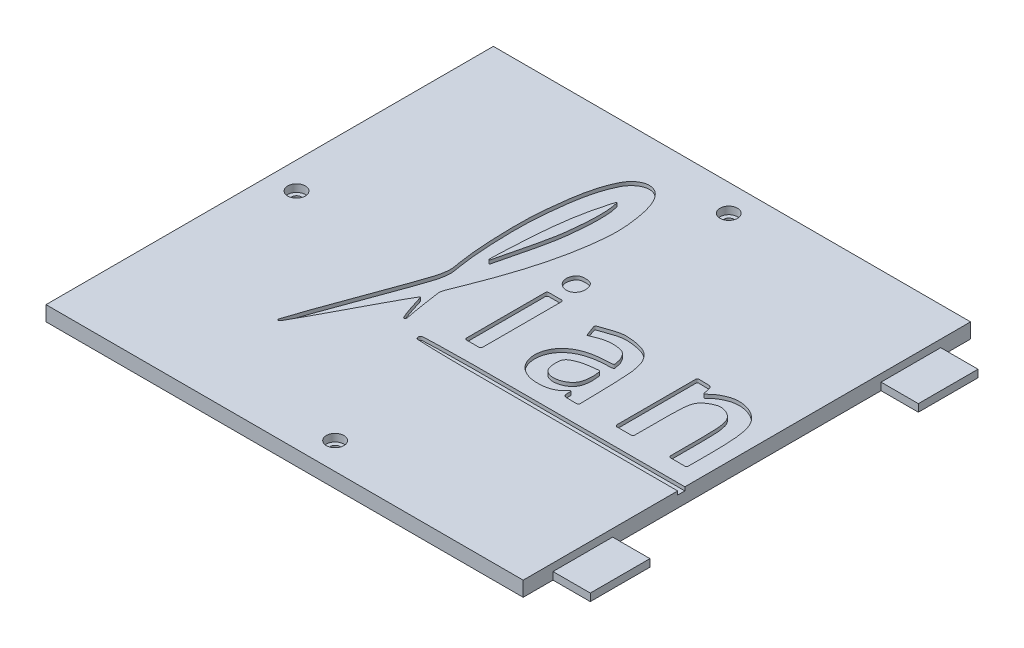
SolidWorks part; units mm, degrees
other "Marca1"
sketch "Croquis4" plane through (-24, 5, 75) normal (0.0144, 0.9293, 0.3691) x (0.9999, -0.0163, 0.0019)
material "PLA"
ref_plane "Alzado" through (0, 0, 0) normal (0, 0, 1) x (1, 0, 0)
ref_plane "Planta" through (0, 0, 0) normal (0, 1, 0) x (1, 0, 0)
ref_plane "Vista lateral" through (0, 0, 0) normal (1, 0, 0) x (0, 0, -1)
sketch "Croquis1" plane through (0, 0, 0) normal (0, 1, 0) x (1, 0, 0)
  line L0 (-327.9437, 75) -> (-327.9437, -75)
  line L1 (-327.9437, 75) -> (-27.9437, 75)
  line L2 (-27.9437, 75) -> (-24, 71.0563)
  line L3 (-327.9437, -75) -> (-27.9437, -75)
  line L4 (-27.9437, -75) -> (-24, -71.0563)
  circle A0 centre (0, 0) radius 75 construction
  arc A1 (-24, 71.0563) -> (-24, -71.0563) centre (0, 0) ccw
  point P0 (0, 0)
  point P6 (-327.9437, 0)
  point P11 (-75, 0)
  point P12 (0, 0)
  dimension "D1" = 150
  dimension "D2" = 150
  dimension "D3" = 300
  dimension "D4" = 135
  dimension "D5" = 24
extrude "Saliente-Extruir1" add sketch "Croquis1" along normal blind 5 contours L1 L2 A1 L4 L3 L0
sketch "Croquis2" plane through (0, 5, 0) normal (0, 1, 0) x (1, 0, 0)
  line L0 (-327.9437, 75) -> (-27.9437, 75) construction
  line L1 (-327.9437, -75) -> (-27.9437, -75) construction
  line L2 (-327.9437, 75) -> (-327.9437, -75) construction
  circle A0 centre (-318.9437, 0) radius 1.6
  circle A1 centre (-240.0037, 66) radius 1.6
  circle A2 centre (-240.0037, -66) radius 1.6
  circle A3 centre (-80.0037, -66) radius 1.6
  circle A4 centre (-80.0037, 66) radius 1.6
  point P10 (0, 0)
  point P12 (0, 0)
  point P13 (0, 0)
  point P14 (0, 0)
  point P15 (0, 0)
  dimension "D1" = 3.2
  dimension "D2" = 9
  dimension "D3" = 9
  dimension "D4" = 9
  dimension "D5" = 160
  dimension "D6" = 87.94
extrude "Cortar-Extruir1" cut sketch "Croquis2" against normal blind 5
sketch "Croquis3" plane through (0, 5, 0) normal (0, 1, 0) x (1, 0, 0)
  circle A0 centre (-240.0037, -66) radius 2.95
  circle A1 centre (-80.0037, -66) radius 2.95
  circle A2 centre (-80.0037, 66) radius 2.95
  circle A3 centre (-240.0037, 66) radius 2.95
  circle A4 centre (-318.9437, 0) radius 2.95
  dimension "D1" = 5.9
extrude "Cortar-Extruir2" cut sketch "Croquis3" against normal blind 2.5
sketch "Croquis5" plane through (0, 5, 0) normal (0, 1, 0) x (1, 0, 0)
  spline S0 degree 3 number of poles 565 (-264.8912, -10.407) -> (-264.8912, -10.407)
  spline S1 degree 3 number of poles 279 (-262.6484, 48.2089) -> (-262.6484, 48.2089)
  spline S2 degree 3 number of poles 493 (-213.5311, -14.7576) -> (-213.5311, -14.7576)
  spline S3 degree 3 number of poles 157 (-225.2653, -4.52) -> (-225.2653, -4.52)
  spline S4 degree 3 number of poles 343 (-98.8163, -23.8618) -> (-98.8163, -23.8618)
  spline S5 degree 3 number of poles 343 (-189.9262, 10.8546) -> (-189.9262, 10.8546)
  spline S6 degree 3 number of poles 380 (-145.717, -14.6405) -> (-145.717, -14.6405)
  spline S7 degree 3 number of poles 125 (-156.8594, -5.2926) -> (-156.8594, -5.2926)
  spline S8 degree 3 number of poles 123 (-242.4618, 21.9905) -> (-242.4618, 21.9905)
  spline S9 degree 3 poles (-242.3565, -0.9911) (-242.3565, 3.3839) (-242.3565, 7.7589) (-242.3565, 12.1339) (-242.3565, 12.24) (-242.3565, 12.4521) (-242.7133, 12.8089) (-242.9254, 12.8089) (-243.0315, 12.8089) (-243.7065, 12.8089) (-244.3815, 12.8089) (-245.0565, 12.8089) (-245.7315, 12.8089) (-246.4065, 12.8089) (-247.0815, 12.8089) (-247.1876, 12.8089) (-247.3997, 12.8089) (-247.7565, 12.4521) (-247.7565, 12.24) (-247.7565, 12.1339) (-247.7565, 7.7589) (-247.7565, 3.3839) (-247.7565, -0.9911) (-247.7565, -5.3661) (-247.7565, -9.7411) (-247.7565, -14.1161) (-247.7565, -14.2221) (-247.7565, -14.4343) (-247.3997, -14.7911) (-247.1876, -14.7911) (-247.0815, -14.7911) (-246.4065, -14.7911) (-245.7315, -14.7911) (-245.0565, -14.7911) (-244.3815, -14.7911) (-243.7065, -14.7911) (-243.0315, -14.7911) (-242.9254, -14.7911) (-242.7133, -14.7911) (-242.3565, -14.4343) (-242.3565, -14.2221) (-242.3565, -14.1161) (-242.3565, -9.7411) (-242.3565, -5.3661) (-242.3565, -0.9911) (-242.3565, 3.3839) (-242.3565, 7.7589) knots -0.203746 0 0 0 0.203746 0.203746 0.203746 0.208686 0.213625 0.218565 0.218565 0.218565 0.25 0.25 0.25 0.281435 0.281435 0.281435 0.286375 0.291314 0.296254 0.296254 0.296254 0.5 0.5 0.5 0.703746 0.703746 0.703746 0.708686 0.713625 0.718565 0.718565 0.718565 0.75 0.75 0.75 0.781435 0.781435 0.781435 0.786375 0.791314 0.796254 0.796254 0.796254 1 1 1 1.203746 1.203746 1.203746 only from (-242.3565, -0.9911) to (-242.3565, -0.9911)
  spline S10 degree 3 number of poles 99 (-100.9338, -21.7323) -> (-100.9338, -21.7323)
extrude "Cortar-Extruir3" cut sketch "Croquis5" against normal blind 1.2
sketch "Croquis6" plane through (0, 5, 0) normal (0, 1, 0) x (1, 0, 0)
  line L0 (-327.9437, 75) -> (-327.9437, -75) construction
  line L1 (-167.9437, -104.5928) -> (32.0563, -104.5928)
  line L2 (-167.9437, -104.5928) -> (-167.9437, 95.4072)
  line L3 (-167.9437, 95.4072) -> (32.0563, 95.4072)
  line L4 (32.0563, -104.5928) -> (32.0563, 95.4072)
  line L5 (-167.9437, -104.5928) -> (32.0563, 95.4072) construction
  line L6 (-167.9437, 95.4072) -> (32.0563, -104.5928) construction
  point P0 (-67.9437, -4.5928)
  point P5 (-278.3273, 0)
  point P8 (-367.9437, 95.4072)
  dimension "D1" = 160
  dimension "D2" = 200
  dimension "D3" = 200
extrude "Cortar-Extruir4" cut sketch "Croquis6" against normal blind 10
sketch "Croquis7" plane through (0, 0, 0) normal (0, -1, 0) x (1, 0, 0)
  line L0 (-167.9437, -75) -> (-167.9437, 75) construction
  line L1 (-180.4437, 65) -> (-155.4437, 65)
  line L2 (-180.4437, 65) -> (-180.4437, 45)
  line L3 (-180.4437, 45) -> (-155.4437, 45)
  line L4 (-155.4437, 65) -> (-155.4437, 45)
  line L5 (-180.4437, 65) -> (-155.4437, 45) construction
  line L6 (-180.4437, 45) -> (-155.4437, 65) construction
  line L7 (-327.9437, 75) -> (-167.9437, 75) construction
  line L8 (-180.4437, -45) -> (-155.4437, -45)
  line L9 (-180.4437, -45) -> (-180.4437, -65)
  line L10 (-180.4437, -65) -> (-155.4437, -65)
  line L11 (-155.4437, -45) -> (-155.4437, -65)
  line L12 (-180.4437, -45) -> (-155.4437, -65) construction
  line L13 (-180.4437, -65) -> (-155.4437, -45) construction
  line L15 (-327.9437, -75) -> (-167.9437, -75) construction
  point P0 (-167.9437, 55)
  point P7 (-167.9437, -55)
  dimension "D1" = 20
  dimension "D2" = 10
  dimension "D3" = 25
  dimension "D4" = 10
extrude "Saliente-Extruir2" add sketch "Croquis7" against normal blind 2.5
